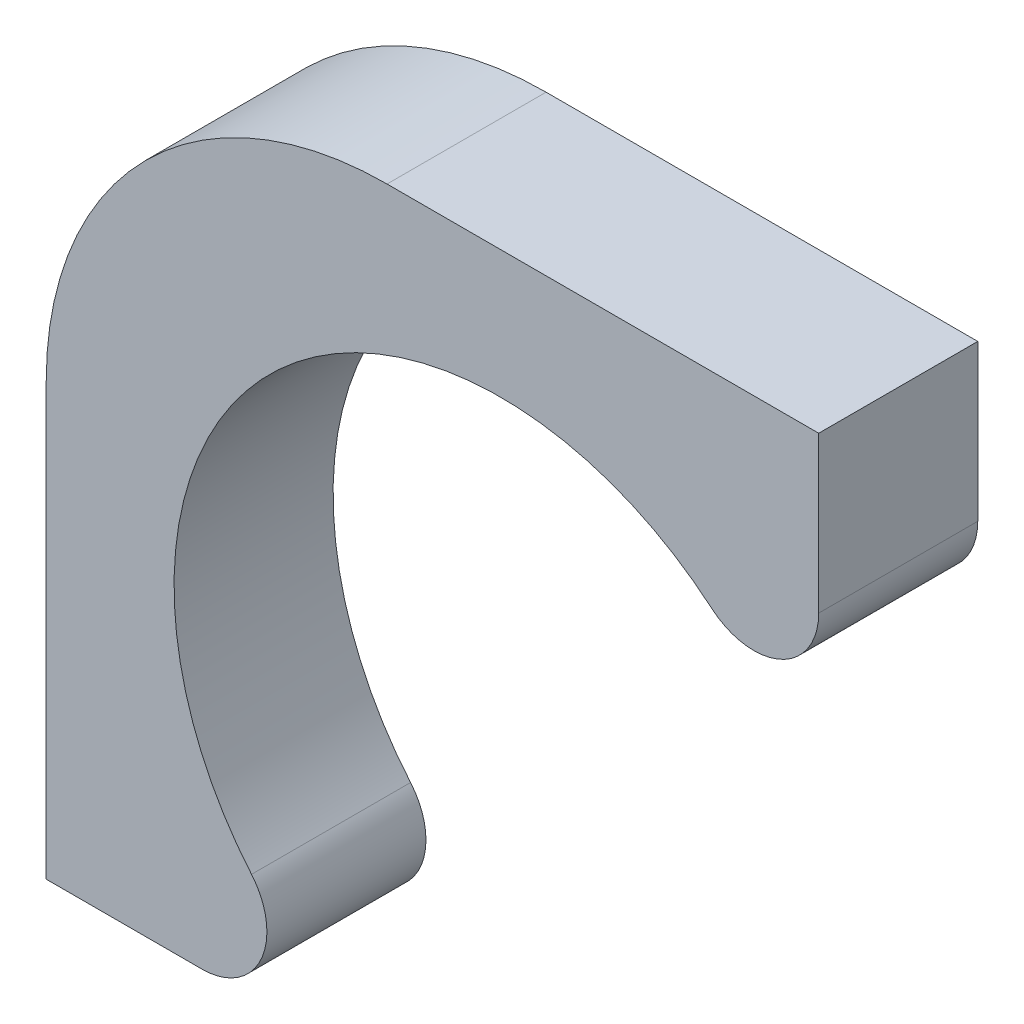
SolidWorks part; units mm, degrees
material "POLIURETANO (11671)"
ref_plane "Alzado" through (0, 0, 0) normal (0, 0, 1) x (1, 0, 0)
ref_plane "Planta" through (0, 0, 0) normal (0, 1, 0) x (1, 0, 0)
ref_plane "Vista lateral" through (0, 0, 0) normal (1, 0, 0) x (0, 0, -1)
sketch "Croquis1" plane through (0, 0, 0) normal (0, 0, 1) x (1, 0, 0)
  line L0 (2.8, 4) -> (-1, 4)
  line L1 (-4, 1) -> (-4, -2.8)
  line L2 (0, 0) -> (0, 4) construction
  line L3 (0, 0) -> (-4, 0) construction
  line L4 (2.8, 4) -> (2.8, 2.6287)
  line L5 (-4, -2.8) -> (-2.6287, -2.8)
  line L6 (2.8, 4) -> (2.8, 2.6287) construction
  arc A0 (-2.1929, -1.8592) -> (1.8592, 2.1929) centre (0, 0) cw
  arc A1 (-1, 4) -> (-4, 1) centre (-1, 1) ccw
  arc A2 (2.8, 2.6287) -> (1.8592, 2.1929) centre (2.2287, 2.6287) cw
  arc A3 (-2.6287, -2.8) -> (-2.1929, -1.8592) centre (-2.6287, -2.2287) ccw
  arc A6 (-1, 4) -> (-4, 1) centre (-1, 1) ccw construction
  point P16 (2.8, 2.9077)
  point P19 (2.2287, 2.0574)
  point P26 (-1, 4)
  point P27 (1.8592, 2.1929)
  point P29 (0, 0)
  dimension "D2" = 4
extrude "Saliente-Extruir1" add sketch "Croquis1" along normal blind 1.4
